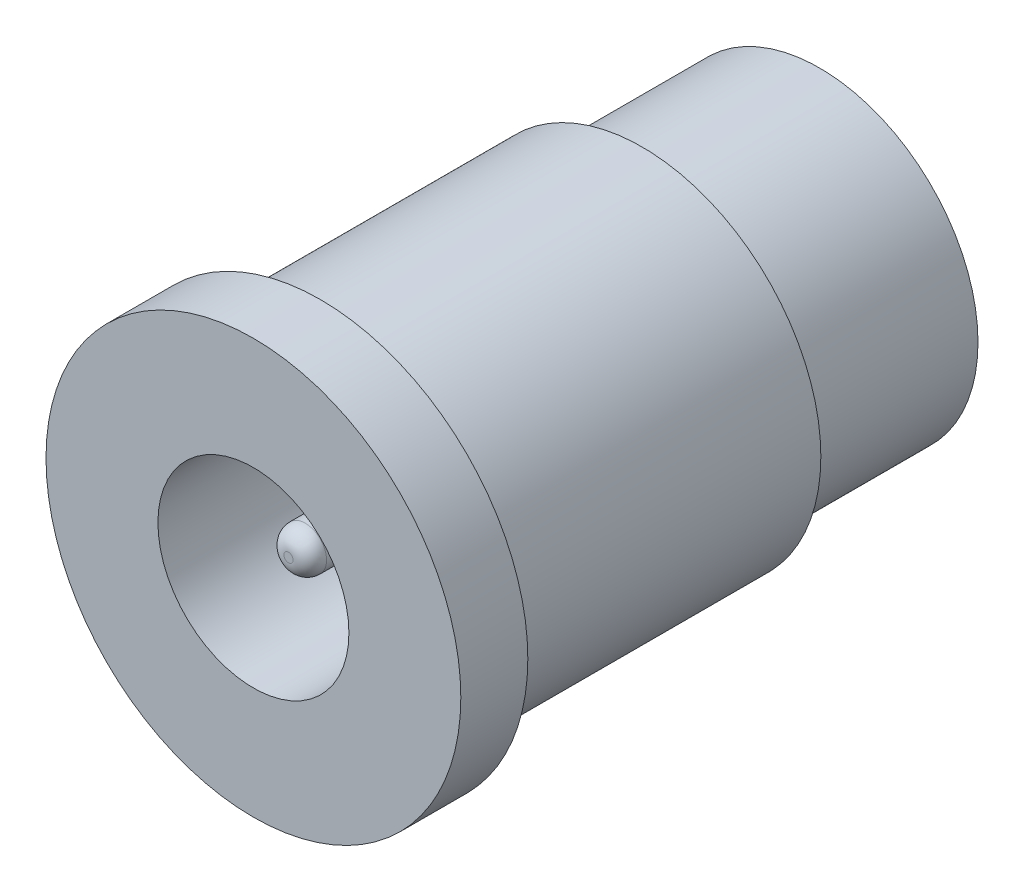
SolidWorks part; units mm, degrees
ref_plane "Front Plane" through (0, 0, 0) normal (0, 0, 1) x (1, 0, 0)
ref_plane "Top Plane" through (0, 0, 0) normal (0, 1, 0) x (1, 0, 0)
ref_plane "Right Plane" through (0, 0, 0) normal (1, 0, 0) x (0, 0, -1)
sketch "Sketch1" plane through (0, 0, 0) normal (1, 0, 0) x (0, 0, -1)
  line L0 (0, 2.85) -> (0, 6.19)
  line L1 (0, 6.19) -> (2, 6.19)
  line L2 (2, 6.19) -> (2, 5.335)
  line L3 (2, 5.335) -> (11.6, 5.335)
  line L4 (11.6, 5.335) -> (11.6, 4.725)
  line L5 (11.6, 4.725) -> (16.9, 4.725)
  line L6 (16.9, 4.725) -> (16.9, 0)
  line L7 (16.9, 0) -> (1.0468, 0)
  line L8 (1.0468, 0) -> (1.0468, 0.1372)
  line L9 (1.5468, 0.6372) -> (11.6, 0.6372)
  line L10 (11.6, 0.6372) -> (11.6, 2.85)
  line L11 (11.6, 2.85) -> (0, 2.85)
  line L12 (-5.0066, 0) -> (-3.0574, 0) construction
  arc A0 (1.0468, 0.1372) -> (1.5468, 0.6372) centre (1.5468, 0.1372) cw
  dimension "D8" = 0.5
  dimension "D1" = 12.38
  dimension "D2" = 10.67
  dimension "D3" = 9.45
  dimension "D4" = 5.7
  dimension "D5" = 2
  dimension "D6" = 5.3
  dimension "D7" = 16.9
revolve "Revolve1" add sketch "Sketch1" angle 360 about L12
